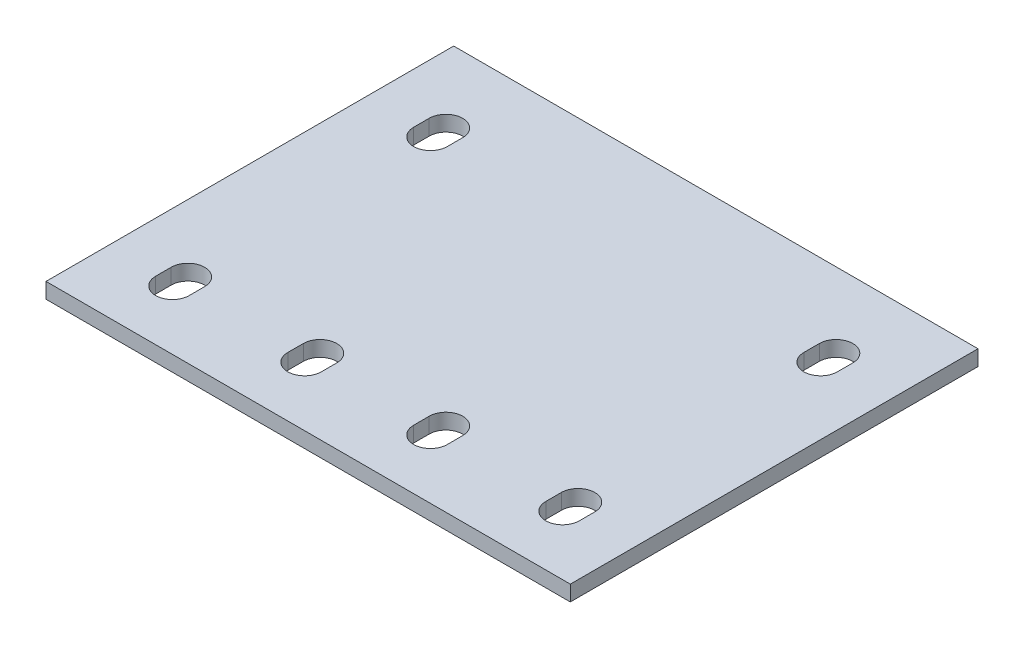
SolidWorks part; units mm, degrees
material "1060 Alloy"
ref_plane "Front Plane" through (0, 0, 0) normal (0, 0, 1) x (1, 0, 0)
ref_plane "Top Plane" through (0, 0, 0) normal (0, 1, 0) x (1, 0, 0)
ref_plane "Right Plane" through (0, 0, 0) normal (1, 0, 0) x (0, 0, -1)
sketch "Sketch1" plane through (0, 0, 0) normal (0, 1, 0) x (1, 0, 0)
  line L0 (32.2274, 1.5) -> (32.2274, -1.5) construction
  line L1 (6.6274, 51.5) -> (6.6274, 48.5) construction
  line L2 (9.8774, 51.5) -> (9.8774, 48.5)
  line L3 (95.2274, -13) -> (-6.3726, -13)
  line L4 (-6.3726, -13) -> (-6.3726, 66)
  line L5 (95.2274, 66) -> (95.2274, -13)
  line L6 (95.2274, 24) -> (-6.3726, 24) construction
  line L7 (3.3774, 51.5) -> (3.3774, 48.5)
  line L8 (44.4274, -13) -> (44.4274, 70.6007) construction
  line L9 (6.6274, 1.5) -> (6.6274, -1.5) construction
  line L10 (9.8774, 1.5) -> (9.8774, -1.5)
  line L11 (3.3774, 1.5) -> (3.3774, -1.5)
  line L12 (56.6274, 1.5) -> (56.6274, -1.5) construction
  line L13 (59.8774, 1.5) -> (59.8774, -1.5)
  line L14 (53.3774, 1.5) -> (53.3774, -1.5)
  line L15 (82.2274, 51.5) -> (82.2274, 48.5) construction
  line L16 (85.4774, 51.5) -> (85.4774, 48.5)
  line L17 (78.9774, 51.5) -> (78.9774, 48.5)
  line L18 (82.2274, 1.5) -> (82.2274, -1.5) construction
  line L19 (78.9774, 1.5) -> (78.9774, -1.5)
  line L20 (85.4774, 1.5) -> (85.4774, -1.5)
  line L21 (-6.3726, 66) -> (95.2274, 66)
  line L22 (28.9774, 1.5) -> (28.9774, -1.5)
  line L23 (35.4774, 1.5) -> (35.4774, -1.5)
  arc A0 (9.8774, 1.5) -> (3.3774, 1.5) centre (6.6274, 1.5) ccw
  arc A1 (3.3774, -1.5) -> (9.8774, -1.5) centre (6.6274, -1.5) ccw
  arc A2 (9.8774, 51.5) -> (3.3774, 51.5) centre (6.6274, 51.5) ccw
  arc A3 (3.3774, 48.5) -> (9.8774, 48.5) centre (6.6274, 48.5) ccw
  arc A4 (78.9774, 1.5) -> (85.4774, 1.5) centre (82.2274, 1.5) cw
  arc A5 (85.4774, -1.5) -> (78.9774, -1.5) centre (82.2274, -1.5) cw
  arc A6 (28.9774, 1.5) -> (35.4774, 1.5) centre (32.2274, 1.5) cw
  arc A7 (35.4774, -1.5) -> (28.9774, -1.5) centre (32.2274, -1.5) cw
  arc A8 (59.8774, 1.5) -> (53.3774, 1.5) centre (56.6274, 1.5) ccw
  arc A9 (53.3774, -1.5) -> (59.8774, -1.5) centre (56.6274, -1.5) ccw
  arc A10 (85.4774, 51.5) -> (78.9774, 51.5) centre (82.2274, 51.5) ccw
  arc A11 (78.9774, 48.5) -> (85.4774, 48.5) centre (82.2274, 48.5) ccw
  point P4 (6.6274, 0)
  point P14 (6.6274, 50)
  point P26 (82.2274, 0)
  point P28 (56.6274, 0)
  point P34 (82.2274, 50)
  point P46 (32.2274, 0)
  dimension "D3" = 13
  dimension "D4" = 50
  dimension "D5" = 63
  dimension "D6" = 50
  dimension "D7" = 13
  dimension "D15" = 3
  dimension "D16" = 3
  dimension "D18" = 6.3726
  dimension "D19" = 3.25
  dimension "D20" = 3.25
  dimension "D21" = 13
  dimension "D8" = 3.25
  dimension "D9" = 3.25
  dimension "D10" = 101.6
  dimension "D11" = 3
  dimension "D12" = 42
  dimension "D13" = 79
  dimension "D14" = 3
  dimension "D17" = 50
  dimension "D23" = 13
  dimension "D24" = 13
extrude "Boss-Extrude1" add sketch "Sketch1" along normal blind 3
